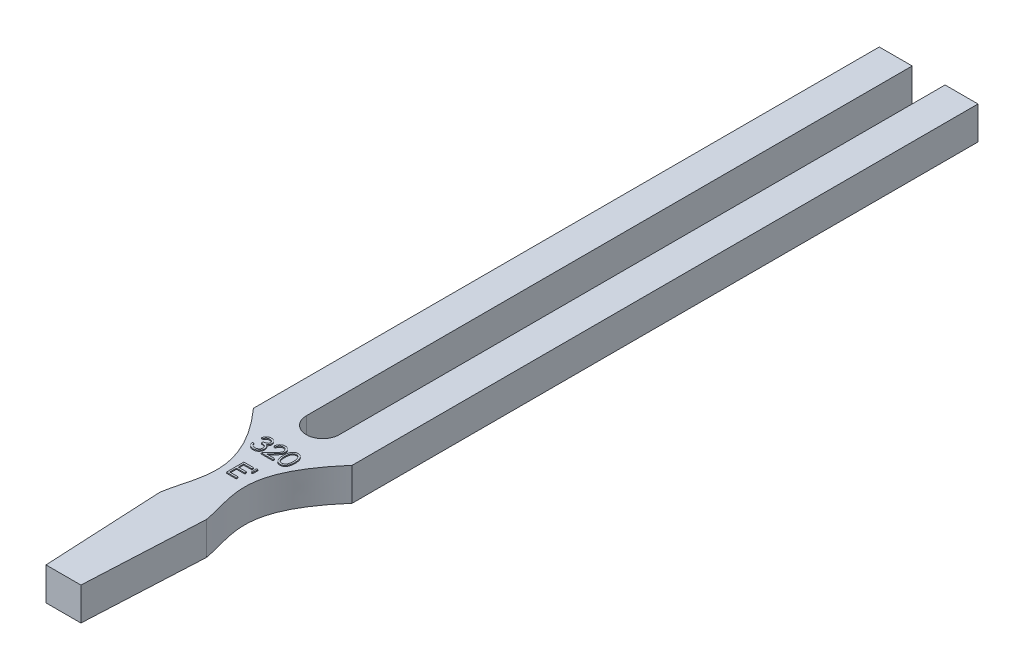
SolidWorks part; units mm, degrees
ref_plane "Front Plane" through (0, 0, 0) normal (0, 0, 1) x (1, 0, 0)
ref_plane "Top Plane" through (0, 0, 0) normal (0, 1, 0) x (1, 0, 0)
ref_plane "Right Plane" through (0, 0, 0) normal (1, 0, 0) x (0, 0, -1)
sketch "Sketch1" plane through (0, 0, 0) normal (0, 1, 0) x (1, 0, 0)
  line L0 (3.3, 0) -> (3.3, 121.5)
  line L1 (-3.3, 0) -> (-3.3, 121.5)
  line L2 (-9.9, 0) -> (-9.9, 121.5)
  line L3 (9.9, 0) -> (9.9, 121.5)
  line L4 (-9.9, 121.5) -> (-3.3, 121.5)
  line L5 (3.3, 121.5) -> (9.9, 121.5)
  line L6 (9.9, 0) -> (9.9, -4)
  line L7 (-9.9, 0) -> (-9.9, -4)
  line L8 (0, -3.3) -> (0, -136.5899) construction
  line L9 (-4.7, -28) -> (4.7, -28)
  line L10 (-3.5, -52) -> (3.5, -52)
  line L11 (-4.7, -28) -> (-3.5, -52)
  line L12 (4.7, -28) -> (3.5, -52)
  circle A0 centre (0, 0) radius 3.3
  spline S0 degree 3 poles (-9.9, -4) (0.8986, -16.0716) (-3.7632, -21.5572) (-4.7, -28) knots 0 0 0 0 1 1 1 1
  spline S1 degree 3 poles (9.9, -4) (-0.6617, -16.1246) (3.4738, -21.2783) (4.7, -28) knots 0 0 0 0 1 1 1 1
  point P15 (0, -18)
  point P18 (0, -28)
  point P19 (-2.75, -18)
  point P25 (0, -52)
extrude "Boss-Extrude1" add sketch "Sketch1" along normal blind 6.6
sketch "Sketch2" plane through (0, 6.6, 0) normal (0, 1, 0) x (1, 0, 0)
  line L0 (-9.607, -4.3302) -> (9.6145, -4.3302) construction
  spline S0 degree 3 poles (9.9, -4) (-0.6617, -16.1246) (3.4738, -21.2783) (4.7, -28) knots 0 0 0 0 1 1 1 1 construction
  spline S1 degree 3 poles (-9.9, -4) (0.8986, -16.0716) (-3.7632, -21.5572) (-4.7, -28) knots 0 0 0 0 1 1 1 1 construction
  text T0 "\r\n320\r\nE'"
extrude "Boss-Extrude2" add sketch "Sketch2" along normal blind 0.2
equation "\"D10@Sketch1\"=2.75"
